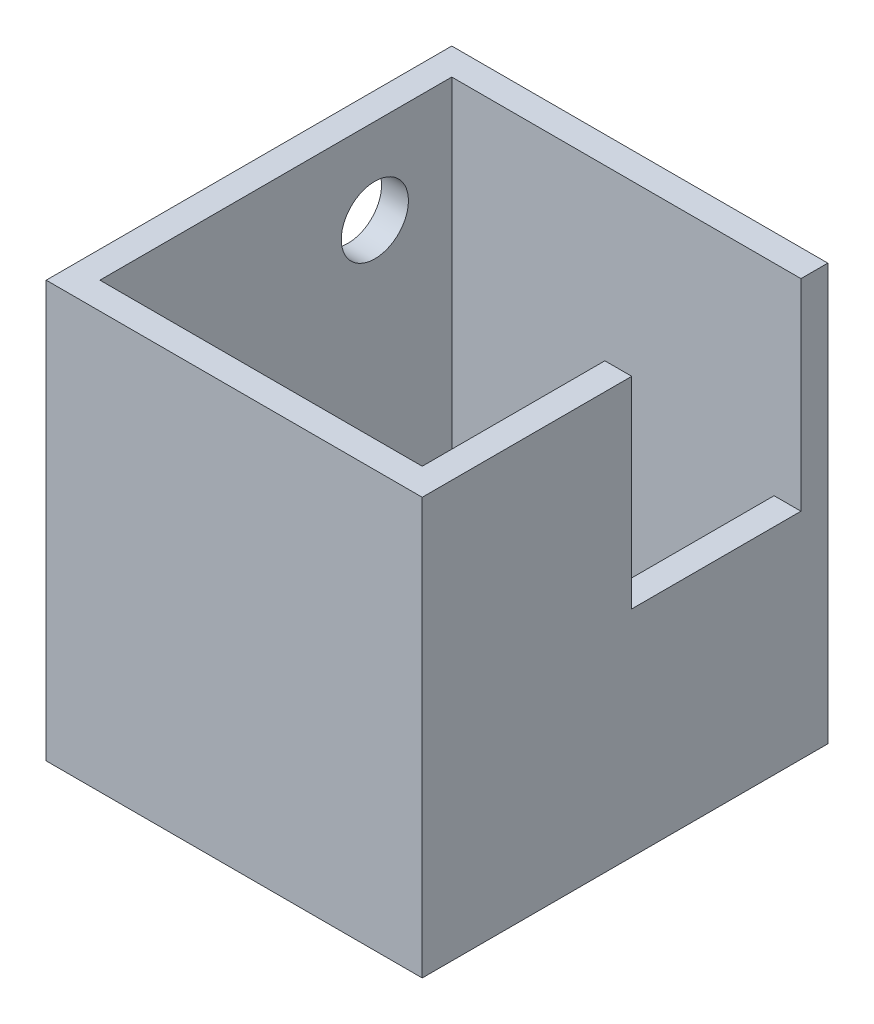
SolidWorks part; units mm, degrees
ref_plane "Plan de face" through (0, 0, 0) normal (0, 0, 1) x (1, 0, 0)
ref_plane "Plan de dessus" through (0, 0, 0) normal (0, 1, 0) x (1, 0, 0)
ref_plane "Plan de droite" through (0, 0, 0) normal (1, 0, 0) x (0, 0, -1)
sketch "Esquisse1" plane through (0, 0, 0) normal (0, 0, 1) x (1, 0, 0)
  line L1 (0, 0) -> (28, 0)
  line L2 (0, 0) -> (0, 31)
  line L3 (0, 31) -> (28, 31)
  line L4 (28, 0) -> (28, 31)
  dimension "D1" = 31
  dimension "D2" = 28
extrude "Boss.-Extru.1" add sketch "Esquisse1" along normal blind 30.2
shell "Coque1" thickness 2
sketch "Esquisse2" plane through (28, 0, 0) normal (1, 0, 0) x (0, 0, -1)
  line L0 (0, 31) -> (-2, 31) construction
  line L1 (-30.2, 31) -> (0, 31) construction
  line L3 (-2, 31) -> (-14.6, 31)
  line L4 (-2, 31) -> (-2, 16)
  line L5 (-2, 16) -> (-14.6, 16)
  line L6 (-14.6, 31) -> (-14.6, 16)
  dimension "D1" = 2
  dimension "D2" = 12.6
  dimension "D3" = 15
extrude "Enlèv. mat.-Extru.1" cut sketch "Esquisse2" against normal up to next
sketch "Esquisse3" plane through (0, 2, 0) normal (0, 1, 0) x (1, 0, 0)
  line L1 (2, -28.2) -> (17, -28.2)
  line L2 (2, -28.2) -> (2, -15.6)
  line L3 (2, -15.6) -> (17, -15.6)
  line L4 (17, -28.2) -> (17, -15.6)
  line L5 (0, -30.2) -> (28, -30.2) construction
  line L6 (2, -28.2) -> (2, -2) construction
  dimension "D1" = 15
  dimension "D2" = 12.6
  dimension "D4" = 2
extrude "Enlèv. mat.-Extru.2" cut sketch "Esquisse3" against normal up to next
sketch "Esquisse4" plane through (0, 2, 0) normal (0, 1, 0) x (1, 0, 0)
  line L0 (0, -30.2) -> (0, 0) construction
  line L1 (2, -14.6) -> (26, -14.6)
  line L2 (2, -14.6) -> (2, -2)
  line L3 (2, -2) -> (26, -2)
  line L4 (26, -14.6) -> (26, -2)
  dimension "D1" = 2
  dimension "D2" = 12.6
extrude "Boss.-Extru.2" add sketch "Esquisse4" along normal blind 1.5
sketch "Esquisse8" plane through (0, 0, 0) normal (-1, 0, 0) x (0, 0, 1)
  line L1 (0, 0) -> (11.8, 0)
  line L2 (0, 0) -> (0, 31)
  line L3 (0, 31) -> (11.8, 31)
  line L4 (11.8, 0) -> (11.8, 31)
  dimension "D1" = 11.8
sketch "Esquisse10" plane through (0, 0, 0) normal (-1, 0, 0) x (0, 0, 1)
  line L1 (0, 0) -> (0, 31) construction
  line L2 (7.7283, 0) -> (7.7283, 24.64) construction
  line L3 (30.2, 0) -> (0, 0) construction
  circle A0 centre (7.7283, 24.64) radius 2.5
  point P0 (7.7283, 0)
  point P1 (7.7283, 3.0366)
  point P2 (7.7283, 2.5499)
  point P3 (7.7283, 0)
  point P10 (7.7283, 5.898)
  point P11 (0, 0)
  dimension "D2" = 5
  dimension "D1" = 7.7283
  dimension "D3" = 24.64
extrude "Enlèv. mat.-Extru.4" cut sketch "Esquisse10" against normal up to next contours A0
sketch "Esquisse5" plane through (2, 0, 0) normal (1, 0, 0) x (0, 0, -1)
  line L1 (-14.6, 3.5) -> (-2, 3.5)
  line L2 (-14.6, 3.5) -> (-14.6, 31)
  line L3 (-14.6, 31) -> (-2, 31)
  line L4 (-2, 3.5) -> (-2, 31)
  point P6 (-13.8, 3.5)
extrude "Boss.-Extru.3" [suppressed] add sketch "Esquisse5" along normal blind 2.3
